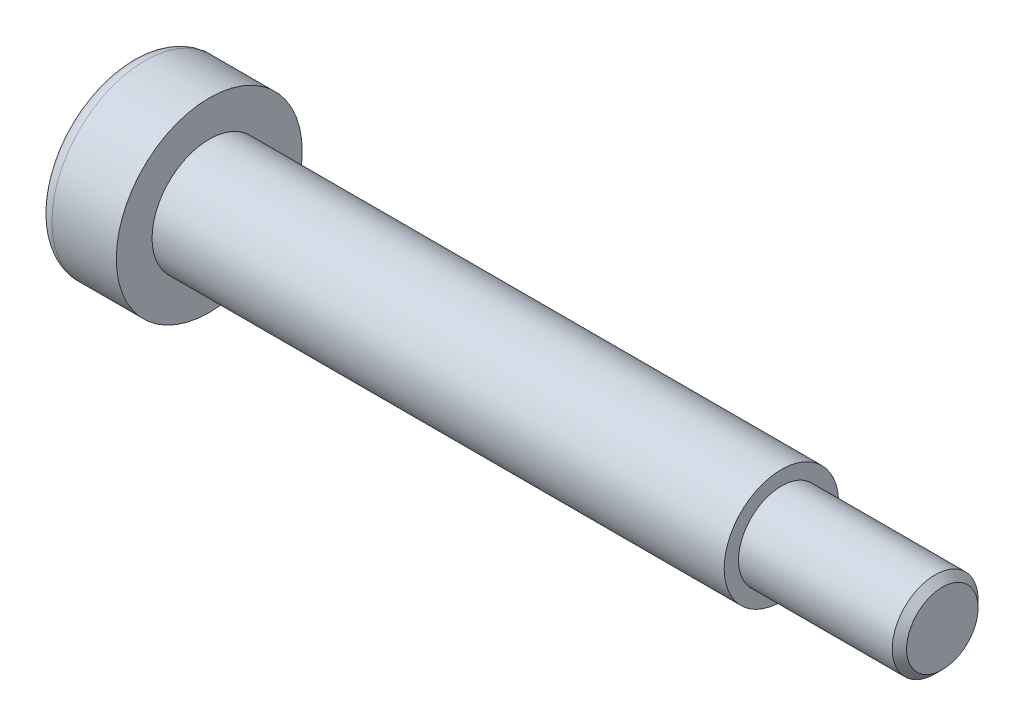
SolidWorks part; units mm, degrees
material "不锈钢 (铁素体)"
ref_plane "前视基准面" through (0, 0, 0) normal (0, 0, 1) x (1, 0, 0)
ref_plane "上视基准面" through (0, 0, 0) normal (0, 1, 0) x (1, 0, 0)
ref_plane "右视基准面" through (0, 0, 0) normal (1, 0, 0) x (0, 0, -1)
sketch "草图1" plane through (0, 0, 0) normal (0, 0, 1) x (1, 0, 0)
  line L0 (0, 0) -> (56.75, 0) construction
  line L1 (0, 0) -> (0, 6.5)
  line L2 (0, 6.5) -> (5.5, 6.5)
  line L3 (5.5, 6.5) -> (5.5, 4)
  line L4 (5.5, 4) -> (45.5, 4)
  line L5 (45.5, 4) -> (45.5, 3)
  line L6 (45.5, 3) -> (56.75, 3)
  line L7 (56.75, 3) -> (56.75, 0)
  line L8 (0, 0) -> (56.75, 0)
  dimension "D1" = 13
  dimension "D2" = 8
  dimension "D3" = 6
  dimension "D4" = 11.25
  dimension "D5" = 5.5
  dimension "D6" = 40
revolve "旋转1" add sketch "草图1" angle 360 about L0
cosmetic thread "装饰螺纹线1" parameters "D2"=4.134
sketch "草图2" plane through (0, 0, 0) normal (-1, 0, 0) x (0, 0, 1)
  line L0 (0, 0) -> (0, 2.3094) construction
  line L1 (0, 2.3094) -> (-2, 1.1547)
  line L2 (-2, 1.1547) -> (-2, -1.1547)
  line L3 (-2, -1.1547) -> (0, -2.3094)
  line L4 (0, -2.3094) -> (2, -1.1547)
  line L5 (2, -1.1547) -> (2, 1.1547)
  line L6 (2, 1.1547) -> (0, 2.3094)
  circle A0 centre (0, 0) radius 2 construction
  dimension "D1" = 4
extrude "切除-拉伸1" cut sketch "草图2" against normal blind 3.3
fillet "圆角1" radius 1 1 edges at (0, 0, 6.5)
chamfer "倒角1" distance 0.5 angle 45 1 edges at (56.75, 0, 3)
